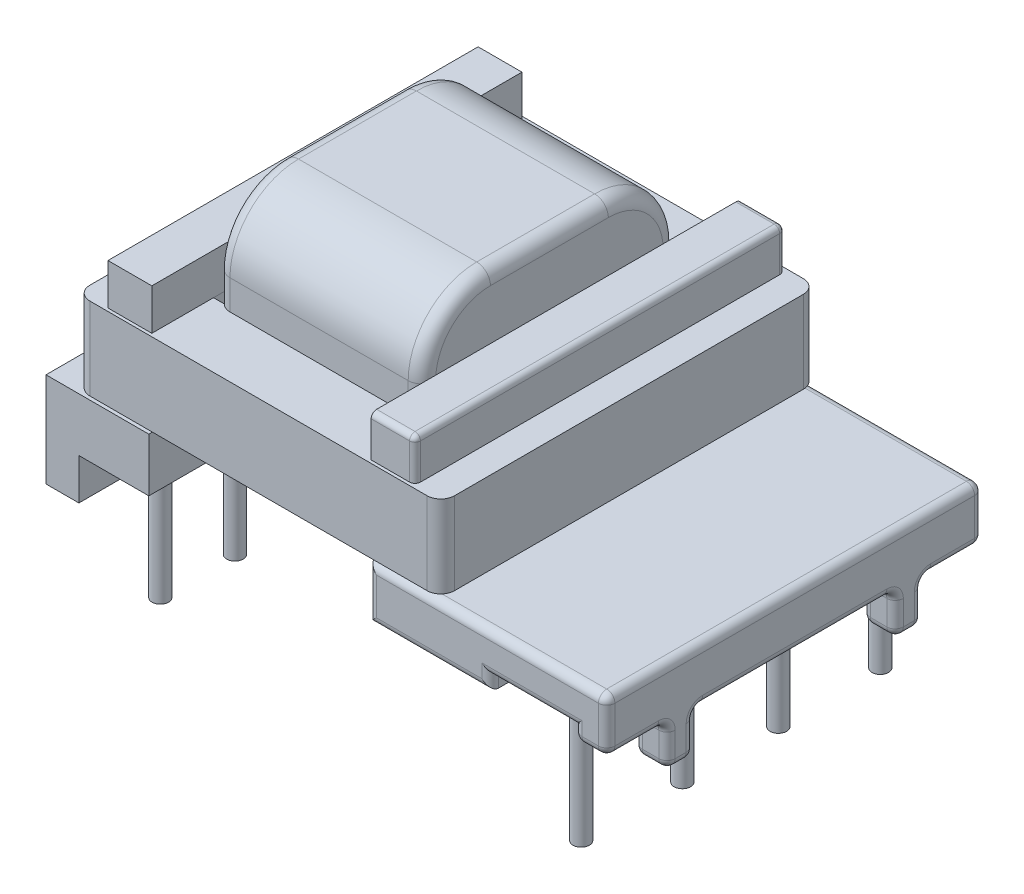
SolidWorks part; units mm, degrees
ref_plane "Front Plane" through (0, 0, 0) normal (0, 0, 1) x (1, 0, 0)
ref_plane "Top Plane" through (0, 0, 0) normal (0, 1, 0) x (1, 0, 0)
ref_plane "Right Plane" through (0, 0, 0) normal (1, 0, 0) x (0, 0, -1)
sketch "Sketch1" plane through (0, 0, 0) normal (0, 1, 0) x (1, 0, 0)
  line L0 (7.675, 5.47) -> (7.675, 1.75) construction
  line L1 (7.675, 1.75) -> (7.675, -1.75) construction
  line L2 (7.675, -1.75) -> (7.675, -5.44) construction
  line L3 (7.675, 0) -> (0, 0) construction
  line L4 (0, 0) -> (-7.675, 0) construction
  line L5 (-7.675, 2.72) -> (-7.675, 0) construction
  line L7 (-7.675, 2.72) -> (-7.675, 5.47) construction
  line L8 (-7.675, 0) -> (-7.675, -2.72) construction
  line L9 (-7.675, -2.72) -> (-7.675, -5.44) construction
  line L10 (7.675, 5.47) -> (-7.675, 5.47) construction
  line L11 (-7.675, -5.44) -> (7.675, -5.44) construction
  circle A0 centre (-7.675, -5.44) radius 0.3
  circle A1 centre (-7.675, -2.72) radius 0.3
  circle A2 centre (-7.675, 0) radius 0.3
  circle A3 centre (-7.675, 5.47) radius 0.3
  circle A4 centre (-7.675, 2.72) radius 0.3
  circle A6 centre (7.675, 5.47) radius 0.3
  circle A7 centre (7.675, 1.75) radius 0.3
  circle A8 centre (7.675, -1.75) radius 0.3
  circle A9 centre (7.675, -5.44) radius 0.3
  dimension "D3" = 2.72
  dimension "D4" = 2.72
  dimension "D5" = 2.72
  dimension "D6" = 0.6
  dimension "D7" = 15.35
  dimension "D1" = 3.5
  dimension "D2" = 2.75
extrude "Boss-Extrude1" add sketch "Sketch1" against normal blind 2.92 and the other way blind 3
sketch "Sketch2" plane through (0, 0, 0) normal (0, 0, 1) x (1, 0, 0)
  line L1 (-10.425, 3.45) -> (10.025, 3.45)
  line L2 (-10.425, 3.45) -> (-10.425, 0)
  line L3 (-10.425, 0) -> (10.025, 0)
  line L4 (10.025, 3.45) -> (10.025, 0)
  dimension "D1" = 20.45
  dimension "D2" = 10.425
  dimension "D3" = 3.45
extrude "Boss-Extrude2" add sketch "Sketch2" along normal mid plane 13.72
sketch "Sketch3" plane through (0, 0, 6.86) normal (0, 0, 1) x (1, 0, 0)
  line L0 (-9.225, 0) -> (-9.225, 1.5)
  line L1 (-9.225, 1.5) -> (5.775, 1.5)
  line L2 (5.775, 1.5) -> (5.775, 2)
  line L3 (5.775, 2) -> (8.825, 2)
  line L4 (8.825, 2) -> (8.825, 0)
  line L5 (8.825, 0) -> (-9.225, 0)
  line L6 (-10.425, 3.45) -> (-10.425, 0) construction
  line L7 (-10.425, 0) -> (10.025, 0) construction
  line L8 (10.025, 0) -> (10.025, 3.45) construction
  dimension "D1" = 1.2
  dimension "D2" = 1.5
  dimension "D3" = 4.25
  dimension "D4" = 0.5
  dimension "D5" = 1.2
extrude "Cut-Extrude1" cut sketch "Sketch3" against normal through all
sketch "Sketch4" plane through (10.025, 0, 0) normal (1, 0, 0) x (0, 0, -1)
  line L0 (-6.86, 0) -> (6.86, 0) construction
  line L1 (-6.86, 0) -> (-4.66, 0)
  line L2 (-6.86, 0) -> (-6.86, 1.5)
  line L3 (-6.86, 1.5) -> (-4.66, 1.5)
  line L4 (-4.66, 0) -> (-4.66, 1.5)
  line L5 (-3.66, 0) -> (3.66, 0)
  line L6 (-3.66, 0) -> (-3.66, 1.5)
  line L7 (-3.66, 1.5) -> (3.66, 1.5)
  line L8 (3.66, 0) -> (3.66, 1.5)
  line L9 (6.86, 0) -> (6.86, 3.45) construction
  line L10 (4.66, 0) -> (6.86, 0)
  line L11 (4.66, 0) -> (4.66, 1.5)
  line L12 (4.66, 1.5) -> (6.86, 1.5)
  line L13 (6.86, 0) -> (6.86, 1.5)
  line L14 (3.66, 1.5) -> (4.66, 1.5) construction
  line L15 (-3.66, 1.5) -> (-4.66, 1.5) construction
  dimension "D1" = 1
  dimension "D2" = 2.2
  dimension "D3" = 1.5
extrude "Cut-Extrude2" cut sketch "Sketch4" against normal blind 2
sketch "Sketch5" plane through (-10.425, 0, 0) normal (-1, 0, 0) x (0, 0, 1)
  line L0 (6.86, 0) -> (-6.86, 0) construction
  line L1 (-5.26, 0) -> (5.26, 0)
  line L2 (-5.26, 0) -> (-5.26, 1.5)
  line L3 (-5.26, 1.5) -> (5.26, 1.5)
  line L4 (5.26, 0) -> (5.26, 1.5)
  line L5 (6.86, 3.45) -> (6.86, 0) construction
  dimension "D1" = 1.5
  dimension "D2" = 1.6
extrude "Cut-Extrude3" cut sketch "Sketch5" against normal blind 2
sketch "Sketch6" plane through (0, 0, 6.86) normal (0, 0, 1) x (1, 0, 0)
  line L1 (-6.675, 5) -> (1.325, 5)
  line L2 (-6.675, 5) -> (-6.675, 0)
  line L3 (-6.675, 0) -> (1.325, 0)
  line L4 (1.325, 5) -> (1.325, 0)
  line L5 (-2.675, 0) -> (-2.675, 6.1367) construction
  dimension "D1" = 8
  dimension "D2" = 2.675
  dimension "D3" = 5
extrude "Cut-Extrude4" cut sketch "Sketch6" against normal through all
ref_plane "Plane1" through (-2.675, 0, 0) normal (1, 0, 0) x (0, 0, -1)
sketch "Sketch7" plane through (-2.675, 0, 0) normal (1, 0, 0) x (0, 0, -1)
  line L0 (0, 0) -> (0, 10.16) construction
  line L1 (-2.15, 10.16) -> (2.15, 10.16)
  line L2 (-4.65, 7.66) -> (-4.65, 2.5)
  line L3 (-2.15, 0) -> (2.15, 0)
  line L4 (4.65, 7.66) -> (4.65, 2.5)
  line L5 (3.66, 0) -> (4.66, 0) construction
  line L6 (0, 5.08) -> (2.7892, 5.08) construction
  arc A0 (2.15, 10.16) -> (4.65, 7.66) centre (2.15, 7.66) cw
  arc A1 (4.65, 2.5) -> (2.15, 0) centre (2.15, 2.5) cw
  arc A2 (-2.15, 0) -> (-4.65, 2.5) centre (-2.15, 2.5) cw
  arc A3 (-4.65, 7.66) -> (-2.15, 10.16) centre (-2.15, 7.66) cw
  point P11 (4.65, 10.16)
  point P14 (4.65, 0)
  point P19 (-4.65, 10.16)
  dimension "D3" = 2.5
  dimension "D1" = 9.3
  dimension "D2" = 10.16
extrude "Boss-Extrude3" add sketch "Sketch7" along normal mid plane 7.5
ref_plane "Plane2" through (0, 5.08, 0) normal (0, 1, 0) x (1, 0, 0)
sketch "Sketch8" plane through (0, 5.08, 0) normal (0, 1, 0) x (1, 0, 0)
  line L0 (1.325, 4.5) -> (-6.675, -4.5) construction
  line L1 (-9.325, 6.86) -> (3.975, 6.86)
  line L2 (-9.325, 6.86) -> (-9.325, -6.86)
  line L3 (-9.325, -6.86) -> (3.975, -6.86)
  line L4 (3.975, 6.86) -> (3.975, -6.86)
  line L5 (-6.675, 4.5) -> (1.325, 4.5)
  line L6 (-6.675, 4.5) -> (-6.675, -4.5)
  line L7 (-6.675, -4.5) -> (1.325, -4.5)
  line L8 (1.325, 4.5) -> (1.325, -4.5)
  line L9 (3.975, -6.86) -> (-9.325, 6.86) construction
  line L10 (-2.675, 2.15) -> (-2.675, 0) construction
  line L11 (1.075, 2.15) -> (-6.425, 2.15) construction
  line L12 (-2.675, -7.194) -> (-2.675, 7.194) construction
  line L13 (0, 0) -> (-2.675, 0) construction
  dimension "D1" = 8
  dimension "D2" = 9
  dimension "D3" = 13.72
  dimension "D4" = 13.3
extrude "Boss-Extrude4" add sketch "Sketch8" along normal mid plane 3
sketch "Sketch9" plane through (0, 0, 0) normal (0, 0, 1) x (1, 0, 0)
  line L0 (-9.325, 6.58) -> (3.975, 6.58) construction
  line L1 (1.325, 6.58) -> (2.925, 6.58)
  line L2 (1.325, 6.58) -> (1.325, 8.08)
  line L3 (1.325, 8.08) -> (2.925, 8.08)
  line L4 (2.925, 6.58) -> (2.925, 8.08)
  line L5 (-6.675, 6.58) -> (-8.275, 6.58)
  line L6 (-6.675, 6.58) -> (-6.675, 8.08)
  line L7 (-6.675, 8.08) -> (-8.275, 8.08)
  line L8 (-8.275, 6.58) -> (-8.275, 8.08)
  dimension "D1" = 1.5
  dimension "D2" = 1.6
  dimension "D3" = 8
  dimension "D4" = 1.325
extrude "Boss-Extrude5" add sketch "Sketch9" along normal mid plane 13.5
sketch "Sketch10" plane through (0, 0, 0) normal (0, 1, 0) x (1, 0, 0)
  circle A0 centre (7.675, -5.44) radius 0.3
  circle A1 centre (7.675, -1.75) radius 0.3
  circle A2 centre (7.675, 1.75) radius 0.3
  circle A3 centre (7.675, 5.47) radius 0.3
  circle A4 centre (-7.675, 5.47) radius 0.3
  circle A5 centre (-7.675, 2.72) radius 0.3
  circle A6 centre (-7.675, 0) radius 0.3
  circle A7 centre (-7.675, -2.72) radius 0.3011
  circle A8 centre (-7.675, -5.44) radius 0.3
extrude "Boss-Extrude6" add sketch "Sketch10" along normal blind 2
fillet "Fillet1" radius 0.3 43 edges at (9.425, 1.5, 4.66) (10.025, 1.5, 5.76) (9.425, 0, 4.66) (10.025, 0.75, 4.66) (9.425, 1.5, 3.66) (10.025, 0.75, 3.66) (9.425, 1.5, -3.66) (10.025, 1.5, 0) (9.425, 0, -3.66) (10.025, 0.75, -3.66) (9.425, 1.5, -4.66) (10.025, 0.75, -4.66) (9.425, 1.5, -6.86) (10.025, 1.5, -5.76) (1.325, 2.475, 6.86) (7.3, 2, 6.86) (9.425, 0, 3.66) (10.025, 0, -4.16) (10.025, 2.475, -6.86) (10.025, 0, 4.16) (5.675, 3.45, -6.86) (10.025, 3.45, 0) (3.55, 1.5, -6.86) (1.325, 2.475, -6.86) (8.825, 1.75, -6.86) (7.3, 2, -6.86) (5.775, 1.75, -6.86) (9.425, 1.5, 6.86) (10.025, 2.475, 6.86) (5.675, 3.45, 6.86) (9.425, 0, -4.66) (8.825, 1.5, -5.76) (8.825, 0.75, -4.66) (8.825, 0, -4.16) (8.825, 0.75, -3.66) (8.825, 1.5, 0) (8.825, 0.75, 3.66) (8.825, 0, 4.16) (8.825, 0.75, 4.66) (8.825, 1.5, 5.76) (8.825, 1.75, 6.86) (5.775, 1.75, 6.86) (3.55, 1.5, 6.86)
fillet "Fillet2" radius 0.2 5 edges at (2.925, 7.33, -6.75) (2.125, 8.08, -6.75) (2.125, 8.08, 6.75) (2.925, 7.33, 6.75) (2.925, 8.08, 0)
fillet "Fillet3" radius 0.5 4 edges at (-9.325, 5.08, -6.86) (-9.325, 5.08, 6.86) (3.975, 5.08, -6.86) (3.975, 5.08, 6.86)
fillet "Fillet4" radius 0.5 16 edges at (-6.425, 0.7322, 3.9178) (-6.425, 0, 0) (1.075, 0.7322, 3.9178) (1.075, 0, 0) (1.075, 9.4278, 3.9178) (1.075, 10.16, 0) (-6.425, 9.4278, -3.9178) (-6.425, 10.16, 0) (-6.425, 0.7322, -3.9178) (1.075, 0.7322, -3.9178) (1.075, 9.4278, -3.9178) (-6.425, 9.4278, 3.9178) (1.075, 5.08, -4.65) (1.075, 5.08, 4.65) (-6.425, 5.08, -4.65) (-6.425, 5.08, 4.65)
equation "\"13.722.92mm\"=2.92"
